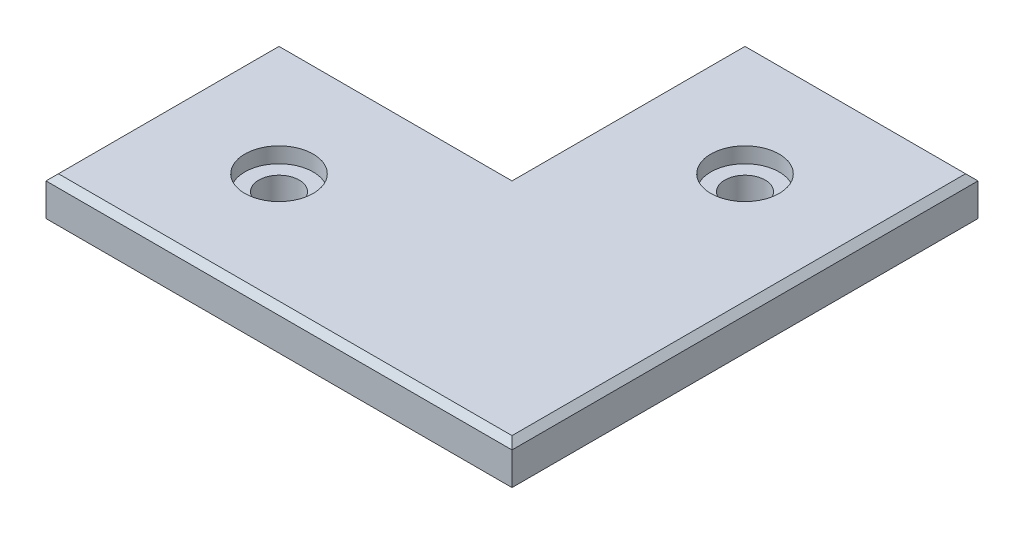
SolidWorks part; units mm, degrees
ref_plane "Front Plane" through (0, 0, 0) normal (0, 0, 1) x (1, 0, 0)
ref_plane "Top Plane" through (0, 0, 0) normal (0, 1, 0) x (1, 0, 0)
ref_plane "Right Plane" through (0, 0, 0) normal (1, 0, 0) x (0, 0, -1)
sketch "Sketch1" plane through (0, 0, 0) normal (0, 1, 0) x (1, 0, 0)
  line L0 (68.9593, -135.0044) -> (68.9593, -96.9044) construction
  line L2 (68.9593, -96.9044) -> (30.8593, -96.9044) construction
  line L4 (30.8593, -135.0044) -> (-7.2407, -135.0044) construction
  line L6 (-7.2407, -135.0044) -> (-7.2407, -173.1044) construction
  line L8 (-7.2407, -173.1044) -> (68.9593, -173.1044)
  line L9 (68.9593, -173.1044) -> (68.9593, -96.9044)
  line L10 (68.9593, -96.9044) -> (30.8593, -96.9044)
  line L11 (30.8593, -96.9044) -> (30.8593, -135.0044)
  line L12 (30.8593, -135.0044) -> (-7.2407, -135.0044)
  line L13 (-7.2407, -135.0044) -> (-7.2407, -173.1044)
extrude "Boss-Extrude1" add sketch "Sketch1" along normal blind 6.35
sketch "Sketch3" plane through (0, 0, 0) normal (0, 1, 0) x (1, 0, 0)
  line L0 (30.8593, -135.0044) -> (68.9593, -135.0044) construction
  line L1 (30.8593, -135.0044) -> (30.8593, -173.1044) construction
  line L2 (-7.2407, -173.1044) -> (68.9593, -173.1044) construction
  line L3 (-7.2407, -154.0544) -> (30.8593, -154.0544) construction
  line L4 (-7.2407, -135.0044) -> (-7.2407, -173.1044) construction
  line L5 (49.9093, -96.9044) -> (49.9093, -135.0044) construction
  line L6 (68.9593, -96.9044) -> (30.8593, -96.9044) construction
  circle A0 centre (11.8093, -154.0544) radius 3.302
  circle A1 centre (49.9093, -115.9544) radius 3.302
extrude "Cut-Extrude2" cut sketch "Sketch3" along normal up to surface (6.35 mm away) up to face at (30.8593, 6.35, 135.0044)
sketch "Sketch4" plane through (0, 6.35, 0) normal (0, 1, 0) x (1, 0, 0)
  circle A0 centre (11.8093, -154.0544) radius 5.588
  circle A1 centre (49.9093, -115.9544) radius 5.588
extrude "Cut-Extrude3" cut sketch "Sketch4" against normal blind 2.54
chamfer "Chamfer1" distance 1.016 6 edges at (68.9593, 6.35, 135.0044) (30.8593, 6.35, 173.1044) (-7.2407, 6.35, 154.0544) (11.8093, 6.35, 135.0044) (30.8593, 6.35, 115.9544) (49.9093, 6.35, 96.9044)
